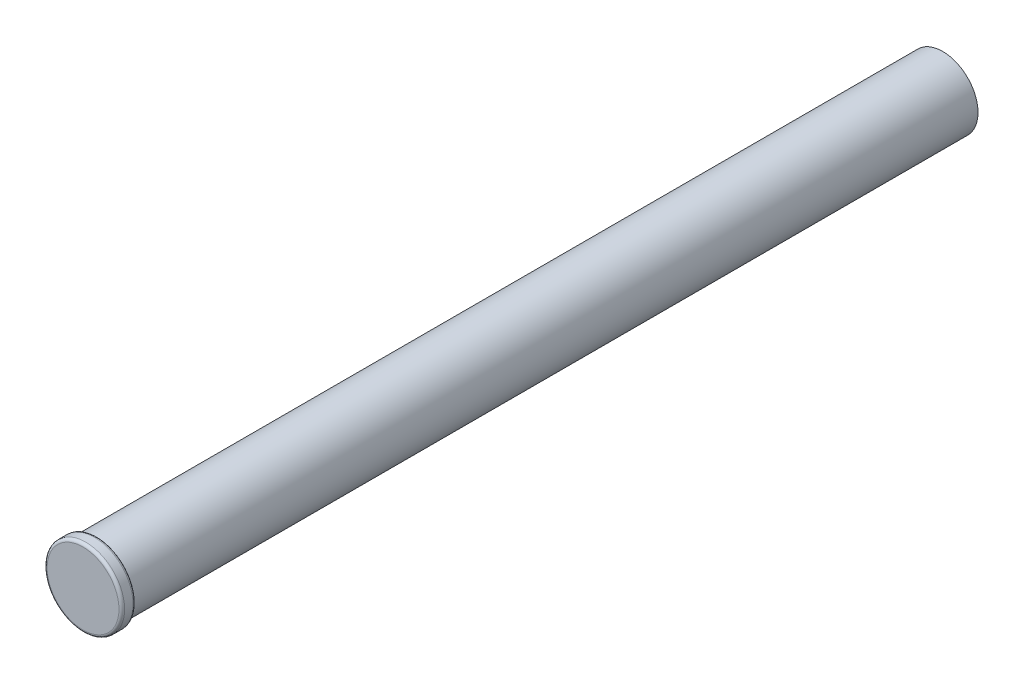
SolidWorks part; units mm, degrees
material "1060 Alloy"
ref_plane "Front Plane" through (0, 0, 0) normal (0, 0, 1) x (1, 0, 0)
ref_plane "Top Plane" through (0, 0, 0) normal (0, 1, 0) x (1, 0, 0)
ref_plane "Right Plane" through (0, 0, 0) normal (1, 0, 0) x (0, 0, -1)
sketch "Sketch2" plane through (0, 0, 0) normal (0, 0, 1) x (1, 0, 0)
  circle A0 centre (0, 0) radius 1.25
  dimension "D1" = 2.5
extrude "Boss-Extrude1" add sketch "Sketch2" along normal blind 30
sketch "Sketch3" plane through (0, 0, 30) normal (0, 0, 1) x (1, 0, 0)
  circle A0 centre (0, 0) radius 1.375
  dimension "D1" = 2.75
extrude "Boss-Extrude2" add sketch "Sketch3" along normal blind 0.5
fillet "Fillet1" radius 0.1 2 edges at (1.375, 0, 30) (1.375, 0, 30.5)
